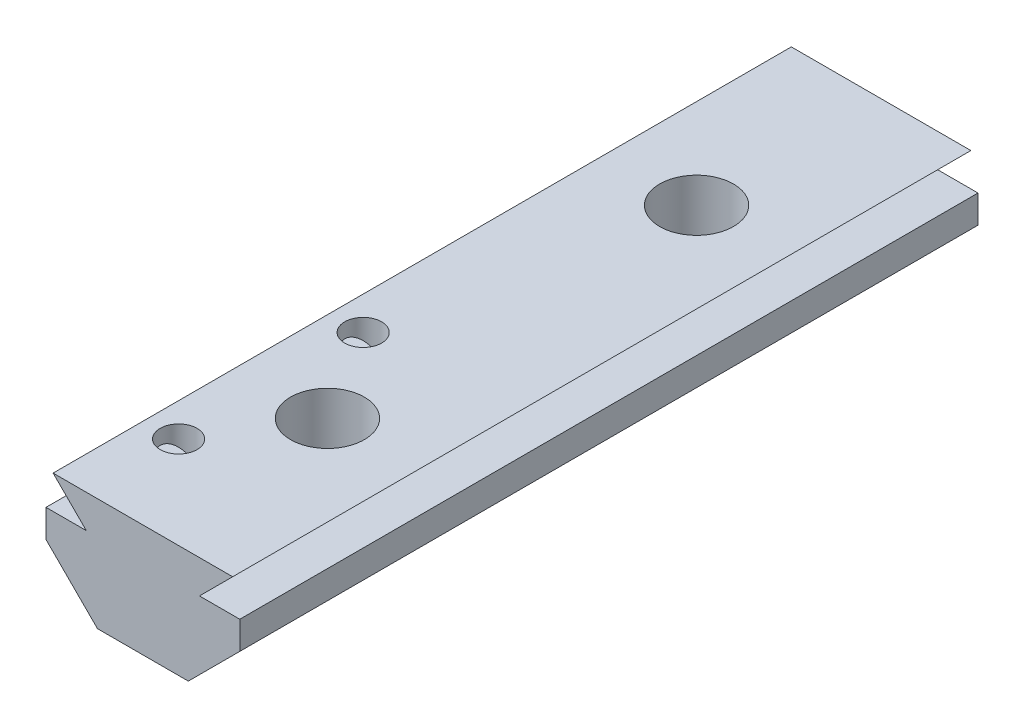
SolidWorks part; units mm, degrees
ref_plane "Front Plane" through (0, 0, 0) normal (0, 0, 1) x (1, 0, 0)
ref_plane "Top Plane" through (0, 0, 0) normal (0, 1, 0) x (1, 0, 0)
ref_plane "Right Plane" through (0, 0, 0) normal (1, 0, 0) x (0, 0, -1)
sketch "Sketch1" plane through (0, 0, 0) normal (0, 0, 1) x (1, 0, 0)
  line L0 (-2.4607, 0) -> (2.4607, 0)
  line L1 (2.4607, 0) -> (5.25, 2.7893)
  line L2 (-2.4607, 0) -> (-5.25, 2.7893)
  line L3 (-5.25, 2.7893) -> (-5.25, 4.3)
  line L4 (5.25, 2.7893) -> (5.25, 4.3)
  line L5 (-5.25, 4.3) -> (-3.065, 4.3)
  line L6 (5.25, 4.3) -> (3.065, 4.3)
  line L7 (-3.065, 4.3) -> (-4.865, 6.1)
  line L8 (3.065, 4.3) -> (4.865, 6.1)
  line L9 (4.865, 6.1) -> (-4.865, 6.1)
  point P4 (0, 0)
  dimension "D1" = 6.13
  dimension "D2" = 10.5
  dimension "D3" = 4.3
  dimension "D4" = 4.3
  dimension "D5" = 1.8
  dimension "D6" = 1.8
extrude "Boss-Extrude1" add sketch "Sketch1" along normal blind 40
sketch "Sketch2" plane through (0, 6.1, 0) normal (0, 1, 0) x (1, 0, 0)
  line L0 (0, 0) -> (0, -40) construction
  line L1 (4.865, 0) -> (-4.865, 0) construction
  line L2 (4.865, -40) -> (-4.865, -40) construction
  circle A0 centre (0, -30) radius 2
  circle A1 centre (0, -10) radius 2
  dimension "D3" = 4
  dimension "D1" = 10
  dimension "D2" = 10
extrude "Cut-Extrude1" cut sketch "Sketch2" against normal through all
sketch "Sketch3" plane through (0, 6.1, 0) normal (0, 1, 0) x (1, 0, 0)
  circle A0 centre (0, -10) radius 3
  circle A1 centre (0, -30) radius 3
  dimension "D1" = 6
sketch "Sketch5" plane through (0, 0, 0) normal (0, -1, 0) x (-1, 0, 0)
  line L1 (-3.2332, -10) -> (-1.6166, -12.8)
  line L2 (-1.6166, -12.8) -> (1.6166, -12.8)
  line L3 (1.6166, -12.8) -> (3.2332, -10)
  line L4 (3.2332, -10) -> (1.6166, -7.2)
  line L5 (1.6166, -7.2) -> (-1.6166, -7.2)
  line L6 (-1.6166, -7.2) -> (-3.2332, -10)
  line L7 (-3.2332, -30) -> (-1.6166, -32.8)
  line L8 (-1.6166, -32.8) -> (1.6166, -32.8)
  line L9 (1.6166, -32.8) -> (3.2332, -30)
  line L10 (3.2332, -30) -> (1.6166, -27.2)
  line L11 (1.6166, -27.2) -> (-1.6166, -27.2)
  line L12 (-1.6166, -27.2) -> (-3.2332, -30)
  circle A0 centre (0, -10) radius 2.8 construction
  circle A1 centre (0, -30) radius 2.8 construction
  dimension "D1" = 5.6
sketch "Sketch8" plane through (0, 0, 40) normal (0, 0, 1) x (1, 0, 0)
  line L0 (-3.065, 4.3) -> (-3.065, 6.1) construction
  line L1 (4.865, 6.1) -> (-4.865, 6.1) construction
sketch "Sketch9" plane through (0, 6.1, 0) normal (0, 1, 0) x (1, 0, 0)
  line L0 (-3.065, -40) -> (-3.065, -35) construction
  line L1 (-3.065, -35) -> (-3.065, -25) construction
  circle A0 centre (-3.065, -35) radius 1
  circle A1 centre (-3.065, -25) radius 1
  dimension "D1" = 2
extrude "Cut-Extrude2" cut sketch "Sketch9" against normal offset from surface (4.1 mm away) 2 up to face at (-2, 0, 30)
